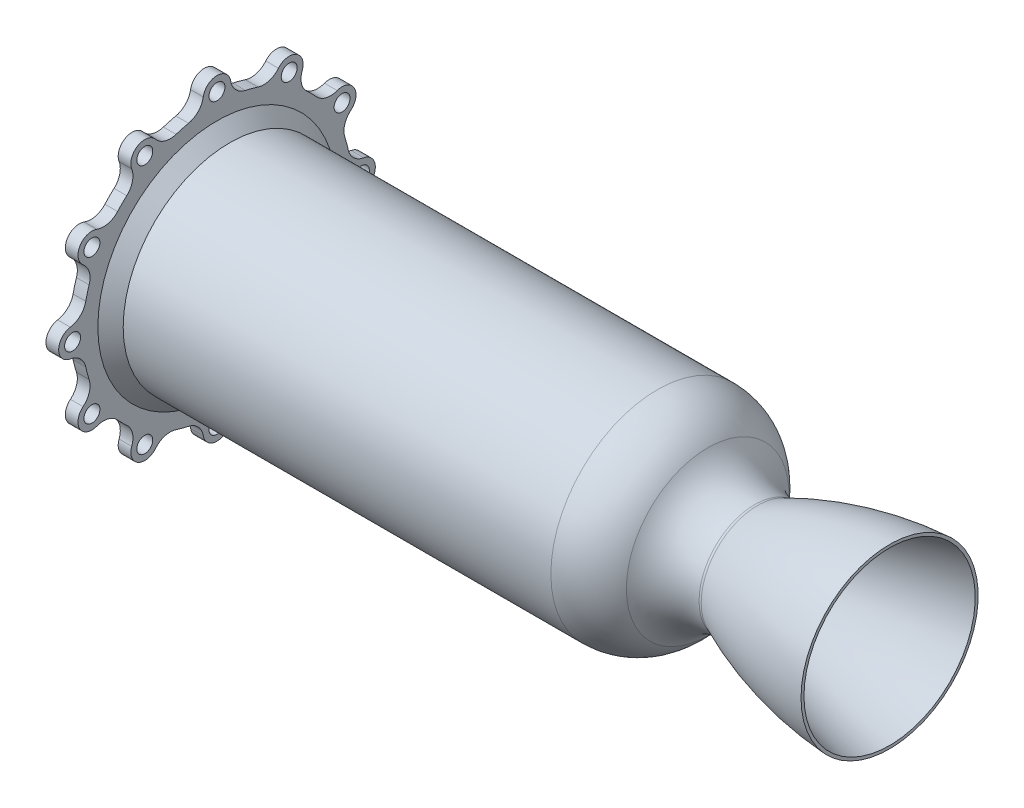
SolidWorks part; units mm, degrees
material "Inconel 718"
ref_plane "Front Plane" through (0, 0, 0) normal (0, 0, 1) x (1, 0, 0)
ref_plane "Top Plane" through (0, 0, 0) normal (0, 1, 0) x (1, 0, 0)
ref_plane "Right Plane" through (0, 0, 0) normal (1, 0, 0) x (0, 0, -1)
sketch "Sketch1" plane through (0, 0, 0) normal (0, 0, 1) x (1, 0, 0)
  line L0 (0, 21.5554) -> (67.3454, 21.5554) construction
  line L1 (0, 0) -> (0, 21.5554) construction
  line L2 (0, 21.5554) -> (0, 31.2726) construction
  line L3 (0, 21.5554) -> (0, 55.883) construction
  line L4 (0, 55.883) -> (0, 89.7945) construction
  line L5 (-275.8922, 0) -> (-275.8922, 59.723) construction
  line L6 (67.6057, 44.4) -> (67.6057, 42.9249)
  line L7 (-275.8922, 50.198) -> (-52.3722, 50.198)
  line L8 (-275.8922, 79.375) -> (-275.8922, 65.438)
  line L9 (-269.5422, 53.373) -> (-48.812, 53.373)
  line L10 (-269.5422, 53.373) -> (-269.5422, 79.375)
  line L11 (-236.4746, 0) -> (92.5965, 0) construction
  line L12 (-269.5422, 79.375) -> (-275.8922, 79.375)
  line L13 (-275.8922, 59.723) -> (-272.7172, 59.723)
  line L14 (-272.7172, 59.723) -> (-272.7172, 53.373)
  line L15 (-272.7172, 53.373) -> (-275.8922, 53.373)
  line L16 (-275.8922, 53.373) -> (-275.8922, 50.198)
  line L17 (-275.8922, 62.898) -> (-273.3522, 62.898)
  line L18 (-273.3522, 62.898) -> (-273.3522, 65.438)
  line L19 (-273.3522, 65.438) -> (-275.8922, 65.438)
  line L20 (-275.8922, 62.898) -> (-275.8922, 59.723)
  arc A0 (0, 21.5554) -> (3.6993, 22.2871) centre (0, 31.2726) ccw
  arc A1 (-28.9029, 37.3625) -> (0, 21.5554) centre (0, 55.883) ccw
  arc A2 (-28.9029, 37.3625) -> (-52.3722, 50.198) centre (-52.3722, 22.3239) ccw
  arc A3 (-23.5564, 40.7885) -> (0, 27.9054) centre (0, 55.883) ccw
  arc A4 (-48.812, 53.373) -> (-23.5564, 40.7885) centre (-48.812, 21.7382) cw
  arc A5 (0, 27.9054) -> (1.3746, 28.1987) centre (0, 31.2726) ccw
  arc A6 (1.3746, 28.1987) -> (67.6057, 44.4) centre (78.8554, -145.0667) cw
  spline S0 degree 4 poles (-2.3078, 19.3755) (-2.1205, 19.4699) (-1.7455, 19.6581) (-1.1811, 19.9396) (-0.4303, 20.3106) (0.3254, 20.6802) (1.0682, 21.0402) (1.8381, 21.4094) (2.5311, 21.7392) (3.5424, 22.2145) (4.0903, 22.4694) (5.427, 23.0866) (6.2853, 23.4736) (7.738, 24.1265) (8.9921, 24.6759) (10.3847, 25.2795) (11.7017, 25.8374) (12.7933, 26.2953) (14.1359, 26.8498) (15.7649, 27.5114) (17.6628, 28.2647) (19.8447, 29.1083) (22.0312, 29.9313) (24.2264, 30.7359) (26.4275, 31.5212) (28.6356, 32.2884) (31.2887, 33.1857) (34.5063, 34.2377) (37.7369, 35.2492) (40.9794, 36.2217) (43.786, 37.0337) (46.0358, 37.667) (48.2904, 38.2846) (50.5486, 38.8863) (52.8118, 39.4729) (55.0771, 40.044) (57.0654, 40.5314) (58.7672, 40.939) (60.1943, 41.2742) (61.3229, 41.5359) (62.4815, 41.8003) (63.5863, 42.0495) (64.7929, 42.3167) (65.8037, 42.5386) (67.374, 42.8763) (68.1776, 43.0465) (70.263, 43.4834) (71.2381, 43.6787) (72.6862, 43.9721) (73.3689, 44.1055) (73.7876, 44.188) (74.0054, 44.2309) knots 0 0 0 0 0 0.01043 0.02086 0.031289 0.041719 0.052023 0.062326 0.072629 0.082933 0.097451 0.111969 0.126487 0.141005 0.170041 0.184559 0.199077 0.213595 0.228113 0.25715 0.286186 0.315222 0.344258 0.373294 0.40233 0.431367 0.460403 0.512468 0.57054 0.599576 0.628612 0.657648 0.686685 0.715721 0.744757 0.773793 0.802829 0.817347 0.831865 0.846383 0.860902 0.87542 0.889938 0.904456 0.918974 0.93923 0.959487 0.979743 0.989872 1 1 1 1 1 construction
  spline S1 degree 4 poles (3.6993, 22.2871) (3.9207, 22.3903) (4.346, 22.5875) (5.427, 23.0866) (6.2853, 23.4736) (7.738, 24.1265) (8.9921, 24.6759) (10.3847, 25.2795) (11.7017, 25.8374) (12.7933, 26.2953) (14.1359, 26.8498) (15.7649, 27.5114) (17.6628, 28.2647) (19.8447, 29.1083) (22.0312, 29.9313) (24.2264, 30.7359) (26.4275, 31.5212) (28.6356, 32.2884) (31.2887, 33.1857) (34.5063, 34.2377) (37.7369, 35.2492) (40.9794, 36.2217) (43.786, 37.0337) (46.0358, 37.667) (48.2904, 38.2846) (50.5486, 38.8863) (52.8118, 39.4729) (55.0771, 40.044) (57.0654, 40.5314) (58.7672, 40.939) (60.1943, 41.2742) (61.3229, 41.5359) (62.4815, 41.8003) (63.5863, 42.0495) (64.7929, 42.3167) (65.8037, 42.5386) (66.8755, 42.7691) (67.3668, 42.8741) (67.6057, 42.9249) knots 0.082933 0.082933 0.082933 0.082933 0.082933 0.097451 0.111969 0.126487 0.141005 0.170041 0.184559 0.199077 0.213595 0.228113 0.25715 0.286186 0.315222 0.344258 0.373294 0.40233 0.431367 0.460403 0.512468 0.57054 0.599576 0.628612 0.657648 0.686685 0.715721 0.744757 0.773793 0.802829 0.817347 0.831865 0.846383 0.860902 0.87542 0.889938 0.904456 0.918974 0.918974 0.918974 0.918974 0.918974
  point P37 (-274.3047, 59.723)
  dimension "D1" = 6.35
  dimension "D3" = 23.4693
  dimension "D5" = 3.175
  dimension "D6" = 21.5554
  dimension "D7" = 42.9249
  dimension "D8" = 343.4979
  dimension "D10" = 31.6348
  dimension "D11" = 3.3673
  dimension "D9" = 189.8003
  dimension "D2" = 223.52
  dimension "D4" = 3.175
  dimension "D12" = 145.0667
  dimension "D13" = 63.9064
  dimension "D14" = 6.35
  dimension "D15" = 79.375
  dimension "D16" = 3.175
  dimension "D17" = 6.35
  dimension "D18" = 50.198
  dimension "D19" = 2.54
  dimension "D20" = 2.54
  dimension "D21" = 3.175
revolve "Revolve1" add sketch "Sketch1" angle 360 about L11
chamfer "Chamfer1" distance 6.35 angle 45 1 edges at (-269.5422, 0, 53.373)
fillet "Fillet1" radius 1.27 4 edges at (-275.8922, 0, 53.373) (-275.8922, 0, 50.198) (-272.7172, 0, 59.723) (-272.7172, 0, 53.373)
sketch "Sketch6" plane through (-275.8922, 0, 0) normal (-1, 0, 0) x (0, 0, 1)
  line L0 (0, 0) -> (0, 106.2653) construction
  circle A0 centre (0, 0) radius 72.39 construction
  point P3 (0, 72.39)
  point P8 (42.5498, 58.5647)
  point P9 (68.847, 22.3697)
  point P10 (68.847, -22.3697)
  point P11 (42.5498, -58.5647)
  point P12 (0, -72.39)
  point P13 (-42.5498, -58.5647)
  point P14 (-68.847, -22.3697)
  point P15 (-68.847, 22.3697)
  point P16 (-42.5498, 58.5647)
  point P17 (0, 0)
  dimension "D1" = 144.78
  dimension "D3" = 22.3697
  dimension "D4" = 68.847
  dimension "D2" = 10
hole_wizard "Hole2" positions "Sketch9" profile "Sketch10" legacy end condition up to next
sketch "Sketch9" plane through (-275.8922, 0, 0) normal (-1, 0, 0) x (0, 0, 1)
  line L0 (0, 0) -> (0, 72.39) construction
  point P0 (0, 72.39)
  dimension "D1" = 72.39
sketch "Sketch10" plane through (-275.8922, 72.39, 0) normal (0, 1, 0) x (0, 0, 1)
  line L0 (0, 0) -> (0, 6.351)
  line L1 (0, 6.351) -> (4, 6.351)
  line L2 (4, 6.351) -> (4, 0)
  line L3 (4, 0) -> (0, 0)
  line L4 (0, 110) -> (0, -10) construction
  dimension "Diameter" = 8
  dimension "Depth" = 6.351
pattern_circular "CirPattern3" count 12 over 360 about axis through (0, 0, 0) along (1, 0, 0) of "Hole2"
sketch "Sketch11" plane through (-275.8922, 0, 0) normal (-1, 0, 0) x (0, 0, 1)
  arc A0 (79.375, 0) -> (73.5318, 6.891) centre (72.39, 0) ccw
  circle A1 centre (0, 0) radius 79.375 construction
  arc A2 (79.375, 0) -> (68.7408, 39.6875) centre (0, 0) ccw
  arc A3 (67.1259, 30.7981) -> (68.7408, 39.6875) centre (62.6916, 36.195) ccw
  circle A4 centre (72.39, 0) radius 4 construction
  arc A5 (65.7802, 14.2688) -> (64.1017, 20.533) centre (0, 0) ccw
  arc A6 (65.7802, 14.2688) -> (73.5318, 6.891) centre (75.0887, 16.2879) ccw
  arc A7 (67.1259, 30.7981) -> (64.1017, 20.533) centre (73.1727, 23.4386) ccw
  circle A8 centre (62.6916, 36.195) radius 4 construction
  point P2 (0, 0)
  point P3 (0, 0)
  dimension "D1" = 19.05
  dimension "D2" = 67.31
extrude "Cut-Extrude1" cut sketch "Sketch11" against normal up to next (6.35 mm away)
pattern_circular "CirPattern4" count 12 over 360 about axis through (0, 0, 0) along (1, 0, 0) of "Cut-Extrude1"
